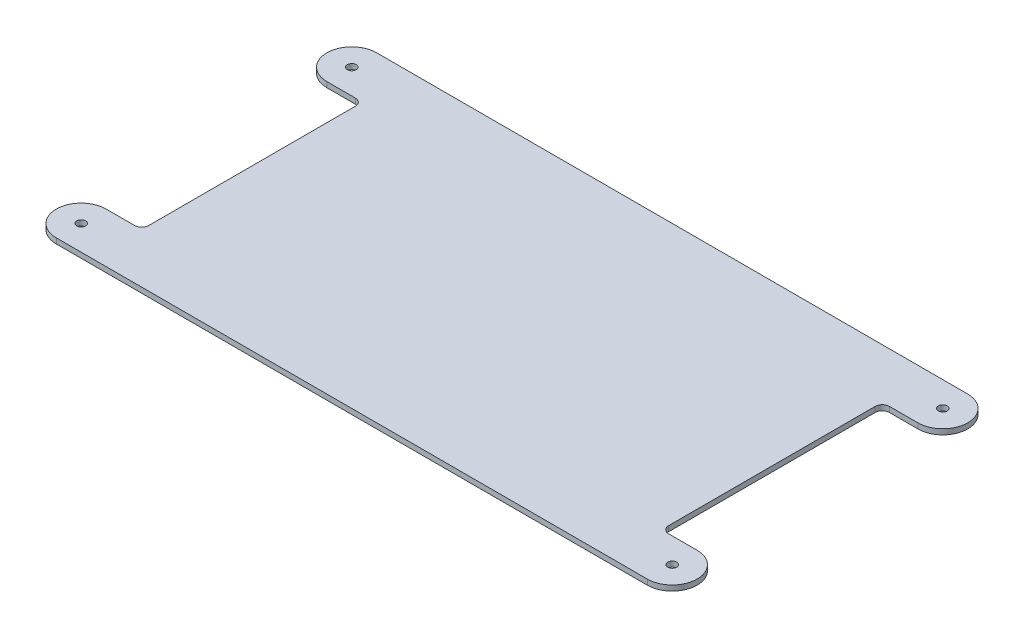
SolidWorks part; units mm, degrees
ref_plane "Front Plane" through (0, 0, 0) normal (0, 0, 1) x (1, 0, 0)
ref_plane "Top Plane" through (0, 0, 0) normal (0, 1, 0) x (1, 0, 0)
ref_plane "Right Plane" through (0, 0, 0) normal (1, 0, 0) x (0, 0, -1)
sketch "Sketch1" plane through (0, 0, 0) normal (0, 1, 0) x (1, 0, 0)
  line L0 (-106.3284, 71.6136) -> (-235.4571, 71.6136)
  line L1 (-106.3284, 71.6136) -> (160.7829, 71.6136)
  line L2 (-210.0571, 30.9736) -> (-210.0571, -116.3464)
  line L3 (-106.3284, -156.9864) -> (160.7829, -156.9864)
  line L4 (160.7829, 30.9736) -> (160.7829, -116.3464)
  line L5 (-215.1371, 36.0536) -> (-235.4571, 36.0536)
  line L6 (160.7829, 71.6136) -> (186.1829, 71.6136)
  line L7 (165.8629, 36.0536) -> (186.1829, 36.0536)
  line L8 (-106.3284, -156.9864) -> (-235.4571, -156.9864)
  line L9 (-215.1371, -121.4264) -> (-235.4571, -121.4264)
  line L10 (160.7829, -156.9864) -> (186.1829, -156.9864)
  line L11 (165.8629, -121.4264) -> (186.1829, -121.4264)
  line L12 (-253.2371, 53.8336) -> (203.9629, 53.8336) construction
  arc A0 (-235.4571, 71.6136) -> (-235.4571, 36.0536) centre (-235.4571, 53.8336) ccw
  arc A1 (-235.4571, -121.4264) -> (-235.4571, -156.9864) centre (-235.4571, -139.2064) ccw
  arc A2 (186.1829, 71.6136) -> (186.1829, 36.0536) centre (186.1829, 53.8336) cw
  arc A3 (186.1829, -121.4264) -> (186.1829, -156.9864) centre (186.1829, -139.2064) cw
  arc A4 (-210.0571, 30.9736) -> (-215.1371, 36.0536) centre (-215.1371, 30.9736) ccw
  arc A5 (-210.0571, -116.3464) -> (-215.1371, -121.4264) centre (-215.1371, -116.3464) cw
  arc A6 (160.7829, 30.9736) -> (165.8629, 36.0536) centre (165.8629, 30.9736) cw
  arc A7 (160.7829, -116.3464) -> (165.8629, -121.4264) centre (165.8629, -116.3464) ccw
  point P24 (-210.0571, 36.0536)
  point P27 (-210.0571, -121.4264)
  dimension "D4" = 17.78
  dimension "D5" = 5.08
  dimension "D1" = 457.2
  dimension "D2" = 228.6
  dimension "D3" = 25.4
extrude "Boss-Extrude1" add sketch "Sketch1" along normal blind 3.81
sketch "Sketch2" plane through (0, 3.81, 0) normal (0, 1, 0) x (1, 0, 0)
  line L0 (-253.2371, 53.8336) -> (-160.2693, 53.8336) construction
  line L1 (-235.4571, 71.6136) -> (-235.4571, 27.1483) construction
  line L2 (203.9629, 53.8336) -> (140.0176, 53.8336) construction
  line L3 (-253.2371, -139.2064) -> (203.9629, -139.2064) construction
  line L4 (186.1829, 71.6136) -> (186.1829, -156.9864) construction
  line L5 (-235.4571, -156.9864) -> (186.1829, -156.9864) construction
  line L6 (-235.4571, -156.9864) -> (-235.4571, 27.1483) construction
  arc A0 (-235.4571, 71.6136) -> (-235.4571, 36.0536) centre (-235.4571, 53.8336) ccw construction
  circle A1 centre (-235.4571, 53.8336) radius 3.175
  arc A2 (186.1829, 36.0536) -> (186.1829, 71.6136) centre (186.1829, 53.8336) ccw construction
  arc A3 (-235.4571, -121.4264) -> (-235.4571, -156.9864) centre (-235.4571, -139.2064) ccw construction
  arc A4 (186.1829, -156.9864) -> (186.1829, -121.4264) centre (186.1829, -139.2064) ccw construction
  circle A5 centre (186.1829, 53.8336) radius 3.175
  circle A6 centre (186.1829, -139.2064) radius 3.175
  circle A7 centre (-235.4571, -139.2064) radius 3.175
  dimension "D1" = 6.35
extrude "Cut-Extrude1" cut sketch "Sketch2" against normal blind 85.852
